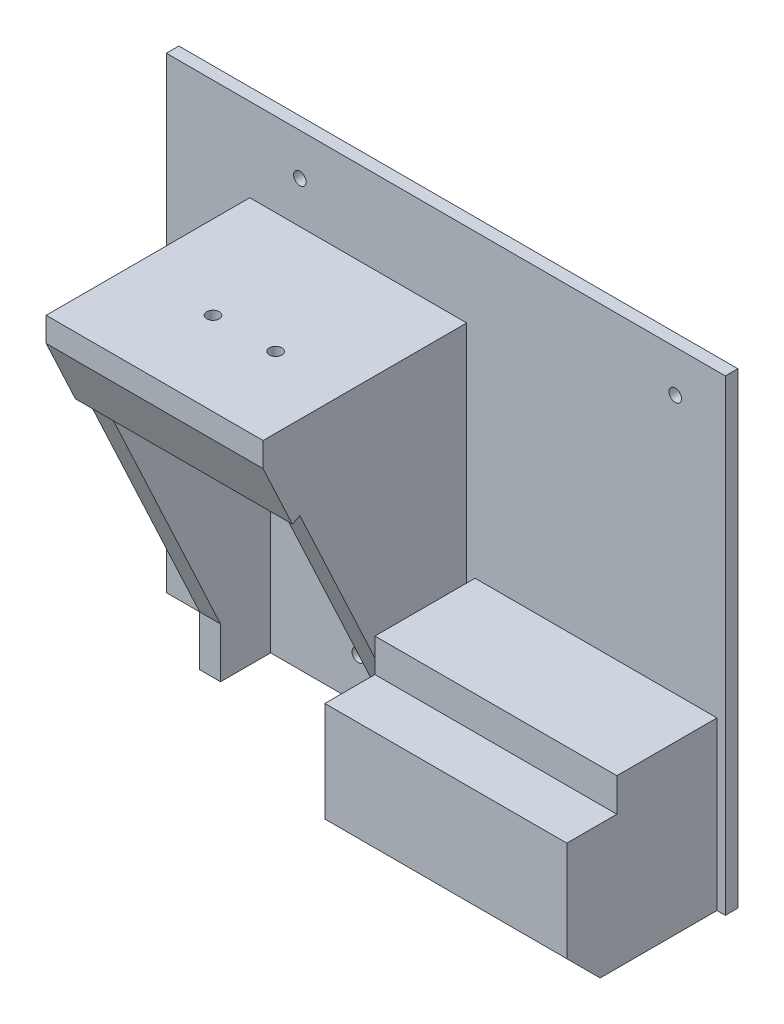
SolidWorks part; units mm, degrees
ref_plane "Front" through (0, 0, 0) normal (0, 0, 1) x (1, 0, 0)
ref_plane "Top" through (0, 0, 0) normal (0, 1, 0) x (1, 0, 0)
ref_plane "Right" through (0, 0, 0) normal (1, 0, 0) x (0, 0, -1)
sketch "Sketch1" plane through (0, 0, 0) normal (0, 0, 1) x (1, 0, 0)
  line L1 (-36, -46) -> (36, -46)
  line L2 (-36, -46) -> (-36, 46)
  line L3 (-36, 46) -> (36, 46)
  line L4 (36, -46) -> (36, 46)
  line L5 (-36, -46) -> (36, 46) construction
  line L6 (-36, 46) -> (36, -46) construction
  point P0 (0, 0)
  dimension "D1" = 92
  dimension "D2" = 72
extrude "Boss-Extrude1" add sketch "Sketch1" along normal blind 3
sketch "Sketch2" plane through (0, 0, 3) normal (0, 0, 1) x (1, 0, 0)
  line L0 (36, 46) -> (-36, 46) construction
  line L1 (36, -46) -> (31, -46)
  line L2 (36, -46) -> (36, 46)
  line L3 (36, 46) -> (31, 46)
  line L4 (31, -46) -> (31, 46)
  line L5 (36, -46) -> (31, 46) construction
  line L6 (36, 46) -> (31, -46) construction
  line L7 (-36, -46) -> (36, -46) construction
  line L8 (-11, -46) -> (-16, -46)
  line L9 (-11, -46) -> (-11, 46)
  line L10 (-11, 46) -> (-16, 46)
  line L11 (-16, -46) -> (-16, 46)
  line L12 (-11, -46) -> (-16, 46) construction
  line L13 (-11, 46) -> (-16, -46) construction
  point P4 (33.5, 0)
  point P12 (-13.5, 0)
  dimension "D1" = 5
  dimension "D2" = 5
  dimension "D3" = 42
extrude "Boss-Extrude2" add sketch "Sketch2" along normal blind 47
sketch "Sketch3" plane through (0, 0, 50) normal (0, 0, 1) x (1, 0, 0)
  line L0 (36, -46) -> (36, 46) construction
  line L1 (-16, 46) -> (36, 46)
  line L2 (-16, 46) -> (-16, 26)
  line L3 (-16, 26) -> (36, 26)
  line L4 (36, 46) -> (36, 26)
  line L5 (-16, 46) -> (36, 26) construction
  line L6 (-16, 26) -> (36, 46) construction
  point P4 (10, 36)
  dimension "D1" = 20
extrude "Boss-Extrude3" add sketch "Sketch3" against normal up to next
sketch "Sketch7" plane through (-16, 0, 0) normal (-1, 0, 0) x (0, 0, 1)
  line L0 (50, 41) -> (15, -34)
  line L1 (50, 46) -> (50, -46) construction
  line L5 (50, 46) -> (3, 46) construction
  line L6 (50, 41) -> (50, -46)
  line L8 (50, -46) -> (50, 26) construction
  line L9 (50, -46) -> (50, 26)
  line L10 (15, -34) -> (15, -46)
  line L11 (50, -46) -> (3, -46) construction
  line L12 (15, -46) -> (50, -46)
  line L14 (3, 46) -> (3, -46) construction
  line M3 (3, -46) -> (50, -46)
  line M4 (50, -46) -> (50, 46)
  dimension "D1" = 12
  dimension "D2" = 5
  dimension "D3" = 12
extrude "Cut-Extrude3" cut sketch "Sketch7" against normal up to next contours L6 L0 M4 M3
sketch "Sketch8" plane through (0, -11.8285, 25.3467) normal (0, -0.4229, 0.9062) x (1, 0, 0)
  line L0 (36, -24.4669) -> (36, 58.2978) construction
  line L1 (-16, 58.2978) -> (36, 58.2978)
  line L2 (-16, 58.2978) -> (-16, 41.7448)
  line L3 (-16, 41.7448) -> (36, 41.7448)
  line L4 (36, 58.2978) -> (36, 41.7448)
  line L5 (-16, 58.2978) -> (36, 41.7448) construction
  line L6 (-16, 41.7448) -> (36, 58.2978) construction
  line L7 (31, 41.7448) -> (-11, 41.7448) construction
  point P4 (10, 50.0213)
extrude "Boss-Extrude5" add sketch "Sketch8" along normal blind 2
sketch "Sketch9" plane through (0, 0, 50) normal (0, 0, 1) x (1, 0, 0)
  line L0 (36, 40.1542) -> (-16, 40.1542) construction
  line L1 (36, 40.1542) -> (-16, 40.1542)
  line L3 (-16, 40.1542) -> (36, 40.1542)
  line L4 (-16, 40.1542) -> (-16, 46)
  line L5 (-16, 46) -> (36, 46)
  line L6 (36, 40.1542) -> (36, 46)
  line L7 (-16, 40.1542) -> (36, 46) construction
  line L8 (-16, 46) -> (36, 40.1542) construction
  point P5 (10, 43.0771)
  line M1 (-16, 41) -> (36, 41)
  line M2 (36, 41) -> (36, 46)
  line M3 (36, 46) -> (-16, 46)
  line M4 (-16, 46) -> (-16, 41)
extrude "Boss-Extrude6" add sketch "Sketch9" along normal up to vertex (1.8124 mm away) contours M4 M1 M2 M3 | L1 L6 L4 M1 up to point (-16, 40.1542, 51.8124)
sketch "Sketch10" plane through (0, 26, 0) normal (0, -1, 0) x (1, 0, 0)
  line L4 (31, 43) -> (-11, 43)
  line L5 (-11, 43) -> (-11, 3)
  line L6 (-11, 3) -> (31, 3)
  line L7 (31, 3) -> (31, 43)
  line L8 (31, 43) -> (-11, 43)
  line L9 (-11, 43) -> (-11, 3)
  line L10 (-11, 3) -> (31, 3)
  line L11 (31, 3) -> (31, 43)
  dimension "D1" = 0
extrude "Cut-Extrude4" cut sketch "Sketch10" against normal blind 17
sketch "Sketch12" plane through (0, 46, 0) normal (0, 1, 0) x (1, 0, 0)
  line L0 (-16, -31.8124) -> (36, -31.8124) construction
  line L1 (-16, -51.8124) -> (-16, -3) construction
  line L2 (36, -51.8124) -> (36, 0) construction
  line L3 (36, -51.8124) -> (-16, -51.8124) construction
  circle A0 centre (4, -31.8124) radius 1.5
  circle A1 centre (19, -31.8124) radius 1.5
  dimension "D2" = 3
  dimension "D3" = 3
  dimension "D4" = 20
  dimension "D5" = 15
  dimension "D1" = 20
extrude "Cut-Extrude5" cut sketch "Sketch12" against normal up to next
sketch "Sketch13" plane through (0, 46, 0) normal (0, 1, 0) x (1, 0, 0)
  line L1 (36, 0) -> (-36, 0)
  line L2 (36, 0) -> (36, -3)
  line L3 (36, -3) -> (-36, -3)
  line L4 (-36, 0) -> (-36, -3)
  line L5 (36, 0) -> (-36, -3) construction
  line L6 (36, -3) -> (-36, 0) construction
  point P4 (0, -1.5)
extrude "Boss-Extrude7" add sketch "Sketch13" along normal blind 20
sketch "Sketch15" plane through (36, 0, 0) normal (1, 0, 0) x (0, 0, -1)
  line L1 (0, -46) -> (-3, -46)
  line L2 (0, -46) -> (0, 66)
  line L3 (0, 66) -> (-3, 66)
  line L4 (-3, -46) -> (-3, 66)
  line L5 (0, -46) -> (-3, 66) construction
  line L6 (0, 66) -> (-3, -46) construction
  point P4 (-1.5, 10)
extrude "Boss-Extrude8" add sketch "Sketch15" along normal blind 62
sketch "Sketch17" plane through (0, 0, 3) normal (0, 0, 1) x (1, 0, 0)
  line L0 (98, -46) -> (36, -46) construction
  line L1 (96, -46) -> (38, -46)
  line L2 (96, -46) -> (96, -6)
  line L3 (96, -6) -> (38, -6)
  line L4 (38, -46) -> (38, -6)
  line L5 (96, -46) -> (38, -6) construction
  line L6 (96, -6) -> (38, -46) construction
  line L7 (98, 66) -> (98, -46) construction
  point P4 (67, -26)
  dimension "D1" = 40
  dimension "D2" = 58
  dimension "D3" = 2
extrude "Boss-Extrude9" add sketch "Sketch17" along normal blind 36
chamfer "Chamfer1" distance 8 angle 45 1 edges at (67, -46, 39)
sketch "Sketch18" plane through (0, 0, 39) normal (0, 0, 1) x (1, 0, 0)
  line L0 (96, -38) -> (96, -6) construction
  line L1 (38, -6) -> (96, -6)
  line L2 (38, -6) -> (38, -14)
  line L3 (38, -14) -> (96, -14)
  line L4 (96, -6) -> (96, -14)
  line L5 (38, -6) -> (96, -14) construction
  line L6 (38, -14) -> (96, -6) construction
  point P4 (67, -10)
  dimension "D1" = 8
extrude "Cut-Extrude8" cut sketch "Sketch18" against normal blind 12
sketch "Sketch14" plane through (0, 0, 3) normal (0, 0, 1) x (1, 0, 0)
  line L0 (-36, 66) -> (98, 66) construction
  line L2 (-11, -46) -> (31, -46) construction
  line L5 (98, 66) -> (98, -46) construction
  line L6 (-36, 66) -> (-36, -46) construction
  line L9 (-11, -46) -> (-11, 43) construction
  circle A0 centre (86, 56) radius 1.5
  circle A1 centre (10, -36) radius 1.5
  circle A2 centre (-4, 56) radius 1.5
  dimension "D1" = 3
  dimension "D4" = 3
  dimension "D6" = 3
  dimension "D7" = 21
  dimension "D8" = 32
  dimension "D2" = 10
  dimension "D3" = 12
  dimension "D5" = 10
extrude "Cut-Extrude9" cut sketch "Sketch14" against normal up to next
